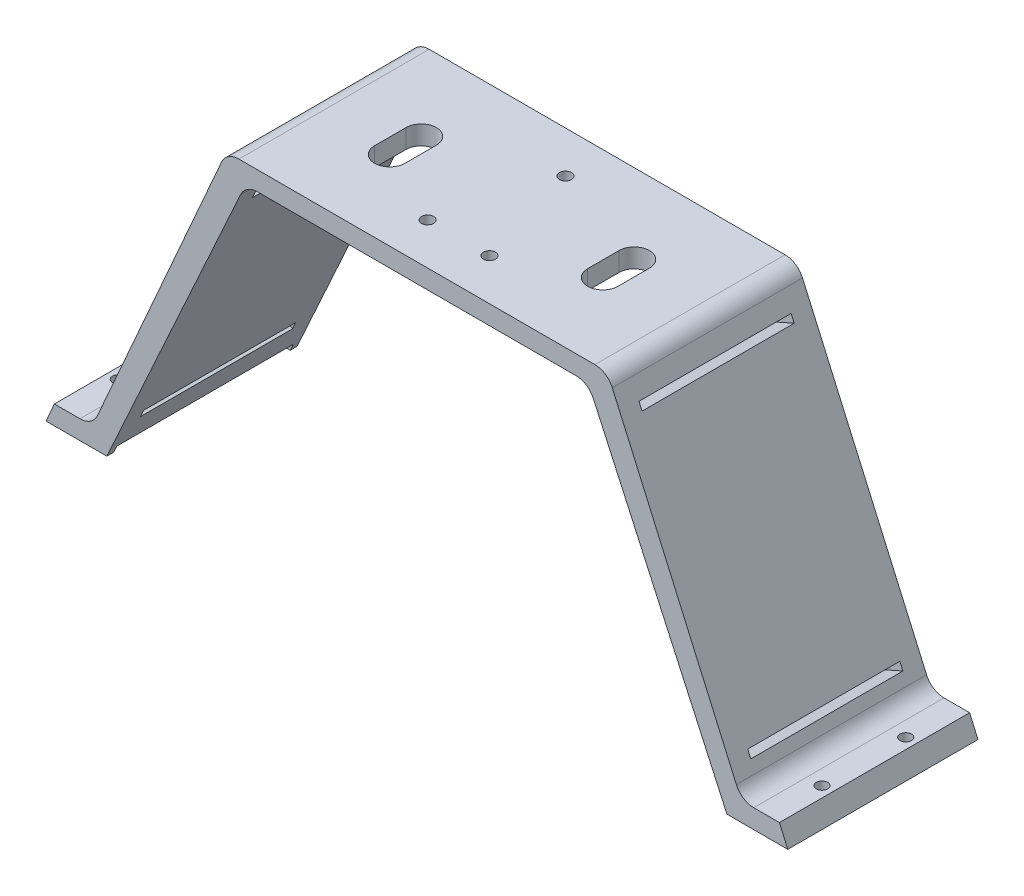
SolidWorks part; units mm, degrees
ref_plane "Front Plane" through (0, 0, 0) normal (0, 0, 1) x (1, 0, 0)
ref_plane "Top Plane" through (0, 0, 0) normal (0, 1, 0) x (1, 0, 0)
ref_plane "Right Plane" through (0, 0, 0) normal (1, 0, 0) x (0, 0, -1)
sketch "Sketch1" plane through (0, 0, 0) normal (0, 0, 1) x (1, 0, 0)
  line L0 (-87.5, 0) -> (87.5, 0)
  line L1 (-87.5, 0) -> (-50.05, 85)
  line L2 (-50.05, 85) -> (50.05, 85)
  line L3 (50.05, 85) -> (87.5, 0)
  point P4 (0, 0)
  dimension "D1" = 175
  dimension "D2" = 100.1
  dimension "D3" = 50.05
  dimension "D4" = 85
extrude "Boss-Extrude2" add sketch "Sketch1" along normal blind 50 contours L1 L2 L3 L0
sketch "Sketch3" plane through (0, 0, 50) normal (0, 0, 1) x (1, 0, 0)
  line L0 (-81.5, 0) -> (81.5, 0)
  line L1 (-87.5, 0) -> (87.5, 0) construction
  line L2 (81.5, 0) -> (45.05, 80)
  line L3 (45.05, 80) -> (-45.05, 80)
  line L4 (-45.05, 80) -> (-81.5, 0)
  line L5 (-50.05, 85) -> (50.05, 85) construction
  dimension "D1" = 163
  dimension "D2" = 6
  dimension "D3" = 90.1
  dimension "D4" = 45.05
  dimension "D5" = 5
extrude "Cut-Extrude1" cut sketch "Sketch3" against normal blind 50
fillet "Fillet1" radius 5 2 edges at (45.05, 80, 25) (-45.05, 80, 25)
sketch "Sketch5" plane through (73.2758, 32.2845, 0) normal (0.9151, 0.4032, 0) x (0, 0, -1)
  line L0 (0, 57.6053) -> (0, -35.2791) construction
  line L1 (-50, -35.2791) -> (0, -35.2791)
  line L2 (-50, -35.2791) -> (-50, -29.8151)
  line L3 (-50, -29.8151) -> (0, -29.8151)
  line L4 (0, -35.2791) -> (0, -29.8151)
  dimension "D1" = 5.464
sketch "Sketch8" plane through (0, 0, 0) normal (0, 1, 0) x (1, 0, 0)
  line L0 (93.2771, -25.8796) -> (149.3121, -25.8796)
sketch "Sketch9" plane through (0, 0, 0) normal (0, 1, 0) x (1, 0, 0)
  line L0 (-93.9767, -25.7952) -> (-133.9417, -25.7952)
sketch "Sketch10" plane through (-73.2758, 32.2845, 0) normal (-0.9151, 0.4032, 0) x (0, 0, 1)
  line L0 (0, -35.2791) -> (0, 57.6053) construction
  line L1 (50, -35.2791) -> (0, -35.2791)
  line L2 (50, -35.2791) -> (50, -29.8191)
  line L3 (50, -29.8191) -> (0, -29.8191)
  line L4 (0, -35.2791) -> (0, -29.8191)
  dimension "D1" = 5.46
extrude "Boss-Extrude4" add sketch "Sketch10" along direction (-1, 0, 0) on the side of the normal blind 10
extrude "Boss-Extrude5" add sketch "Sketch5" along direction (1, 0, 0) on the side of the normal blind 10 contours L3 L4 L1 L2
sketch "Sketch11" plane through (0, 4.9965, 0) normal (0, 1, 0) x (1, 0, 0)
  line L0 (-97.5, 0) -> (-97.5, -50) construction
  line L1 (-95.2986, -50) -> (-85.2986, -50) construction
  circle A0 centre (-92.5, -14) radius 1.5
  circle A1 centre (-92.5, -36) radius 1.5
  dimension "D1" = 22
  dimension "D2" = 5
  dimension "D3" = 14
extrude "Cut-Extrude2" cut sketch "Sketch11" against normal blind 10
sketch "Sketch12" plane through (0, 5.0002, 0) normal (0, 1, 0) x (1, 0, 0)
  line L0 (97.5, -50) -> (97.5, 0) construction
  line L1 (95.297, -50) -> (85.297, -50) construction
  circle A0 centre (92.5, -14) radius 1.5
  circle A1 centre (92.5, -36) radius 1.5
  dimension "D1" = 22
  dimension "D2" = 5
  dimension "D3" = 14
extrude "Cut-Extrude3" cut sketch "Sketch12" against normal blind 10
fillet "Fillet2" radius 5 2 edges at (85.297, 5.0002, 25) (-85.2986, 4.9965, 25)
fillet "Fillet3" radius 5 2 edges at (50.05, 85, 25) (-50.05, 85, 25)
sketch "Sketch13" plane through (0, 85, 0) normal (0, 1, 0) x (1, 0, 0)
  line L1 (-46.7892, 0) -> (-46.7892, -50) construction
  line L2 (-46.7892, 0) -> (46.7892, 0) construction
  circle A0 centre (0.0008, -10.945) radius 1.6
  circle A2 centre (-8.1292, -39.055) radius 1.6
  circle A3 centre (8.1308, -39.055) radius 1.6
  dimension "D1" = 3.2
  dimension "D2" = 3.2
  dimension "D3" = 3.2
  dimension "D4" = 16.26
  dimension "D5" = 46.79
  dimension "D6" = 28.11
  dimension "D7" = 8.13
  dimension "D8" = 10.945
sketch "Sketch15" plane through (0, 85, 0) normal (0, 1, 0) x (1, 0, 0)
  line L0 (-27.9992, -20.87) -> (-27.9992, -29.13) construction
  line L1 (-23.9992, -20.87) -> (-23.9992, -29.13)
  line L2 (-31.9992, -20.87) -> (-31.9992, -29.13)
  line L3 (28.0008, -20.87) -> (28.0008, -29.13) construction
  line L4 (32.0008, -20.87) -> (32.0008, -29.13)
  line L5 (24.0008, -20.87) -> (24.0008, -29.13)
  line L6 (-46.7892, 0) -> (46.7892, 0) construction
  line L7 (-46.7892, -50) -> (46.7892, -50) construction
  arc A0 (-23.9992, -20.87) -> (-31.9992, -20.87) centre (-27.9992, -20.87) ccw
  arc A1 (-31.9992, -29.13) -> (-23.9992, -29.13) centre (-27.9992, -29.13) ccw
  arc A2 (32.0008, -20.87) -> (24.0008, -20.87) centre (28.0008, -20.87) ccw
  arc A3 (24.0008, -29.13) -> (32.0008, -29.13) centre (28.0008, -29.13) ccw
  point P2 (-27.9992, -25)
  point P7 (28.0008, -25)
  point P14 (28.0008, -16.87)
  dimension "D5" = 20.87
  dimension "D1" = 4
  dimension "D2" = 4
  dimension "D6" = 20.87
  dimension "D7" = 20.87
  dimension "D8" = 20.87
extrude "Cut-Extrude8" cut sketch "Sketch15" against normal blind 8.5
sketch "Sketch16" plane through (73.2758, 32.2845, 0) normal (0.9151, 0.4032, 0) x (0, 0, -1)
  line L2 (-45, 49.3444) -> (-5, 49.3444)
  line L3 (-45, 49.3444) -> (-45, 47.3444)
  line L4 (-45, 47.3444) -> (-5, 47.3444)
  line L5 (-5, 49.3444) -> (-5, 47.3444)
  line L6 (0, 54.3444) -> (0, -26.5542) construction
  line L7 (0, 54.3444) -> (-50, 54.3444) construction
  line L8 (-50, -26.5542) -> (0, -26.5542) construction
  line L9 (-45, -23.5542) -> (-5, -23.5542)
  line L10 (-45, -23.5542) -> (-45, -21.5542)
  line L11 (-45, -21.5542) -> (-5, -21.5542)
  line L12 (-5, -23.5542) -> (-5, -21.5542)
  line L13 (-50, 54.3444) -> (-50, -26.5542) construction
  point P14 (-45, -22.5542)
  dimension "D1" = 40
  dimension "D2" = 5
  dimension "D3" = 5
  dimension "D4" = 2
  dimension "D5" = 2
  dimension "D6" = 40
  dimension "D7" = 3
  dimension "D8" = 5
sketch "Sketch17" plane through (-73.2758, 32.2845, 0) normal (-0.9151, 0.4032, 0) x (0, 0, 1)
  line L2 (0, -26.5582) -> (0, 54.3444) construction
  line L3 (5, 49.3444) -> (45, 49.3444)
  line L4 (5, 49.3444) -> (5, 47.3444)
  line L5 (5, 47.3444) -> (45, 47.3444)
  line L6 (45, 49.3444) -> (45, 47.3444)
  line L7 (50, 54.3444) -> (0, 54.3444) construction
  line L8 (0, -26.5582) -> (50, -26.5582) construction
  line L9 (5, -23.5582) -> (45, -23.5582)
  line L10 (5, -23.5582) -> (5, -21.5582)
  line L11 (5, -21.5582) -> (45, -21.5582)
  line L12 (45, -23.5582) -> (45, -21.5582)
  dimension "D1" = 40
  dimension "D2" = 2
  dimension "D3" = 5
  dimension "D4" = 5
  dimension "D5" = 40
  dimension "D6" = 2
  dimension "D7" = 3
  dimension "D8" = 5
sketch "Sketch18" plane through (0, 0, 0) normal (0, -1, 0) x (1, 0, 0)
  line L0 (81.5, 0) -> (97.5, 0) construction
  line L1 (95.7, 1.8) -> (80.5, 1.8)
  line L2 (95.7, 1.8) -> (95.7, 48.2)
  line L3 (95.7, 48.2) -> (80.5, 48.2)
  line L4 (80.5, 1.8) -> (80.5, 48.2)
  line L5 (97.5, 50) -> (97.5, 0) construction
  line L6 (81.5, 50) -> (97.5, 50) construction
  dimension "D1" = 1.8
  dimension "D2" = 1.8
  dimension "D3" = 1.8
  dimension "D4" = 15.2
extrude "Cut-Extrude14" cut sketch "Sketch18" against normal blind 1.8 contours L1 L4 L3 L2
sketch "Sketch19" plane through (0, 0, 0) normal (0, -1, 0) x (1, 0, 0)
  line L0 (-97.5, 0) -> (-81.5, 0) construction
  line L1 (-95.7, 1.8) -> (-80.5, 1.8)
  line L2 (-95.7, 1.8) -> (-95.7, 48.2)
  line L3 (-95.7, 48.2) -> (-80.5, 48.2)
  line L4 (-80.5, 1.8) -> (-80.5, 48.2)
  line L5 (-97.5, 0) -> (-97.5, 50) construction
  line L6 (-97.5, 50) -> (-81.5, 50) construction
  dimension "D1" = 1.8
  dimension "D2" = 1.8
  dimension "D3" = 1.8
  dimension "D4" = 15.2
extrude "Cut-Extrude15" cut sketch "Sketch19" against normal blind 1.8
extrude "Cut-Extrude16" cut sketch "Sketch16" against normal blind 10
extrude "Cut-Extrude17" cut sketch "Sketch17" against normal blind 10
extrude "Cut-Extrude18" cut sketch "Sketch13" against normal blind 10
sketch "Sketch20" plane through (0, 80, 0) normal (0, -1, 0) x (1, 0, 0)
  circle A0 centre (-8.1292, 39.055) radius 2.5
  circle A1 centre (8.1308, 39.055) radius 2.5
  circle A2 centre (0.0008, 10.945) radius 2.5
extrude "Cut-Extrude19" cut sketch "Sketch20" against normal blind 1.5
